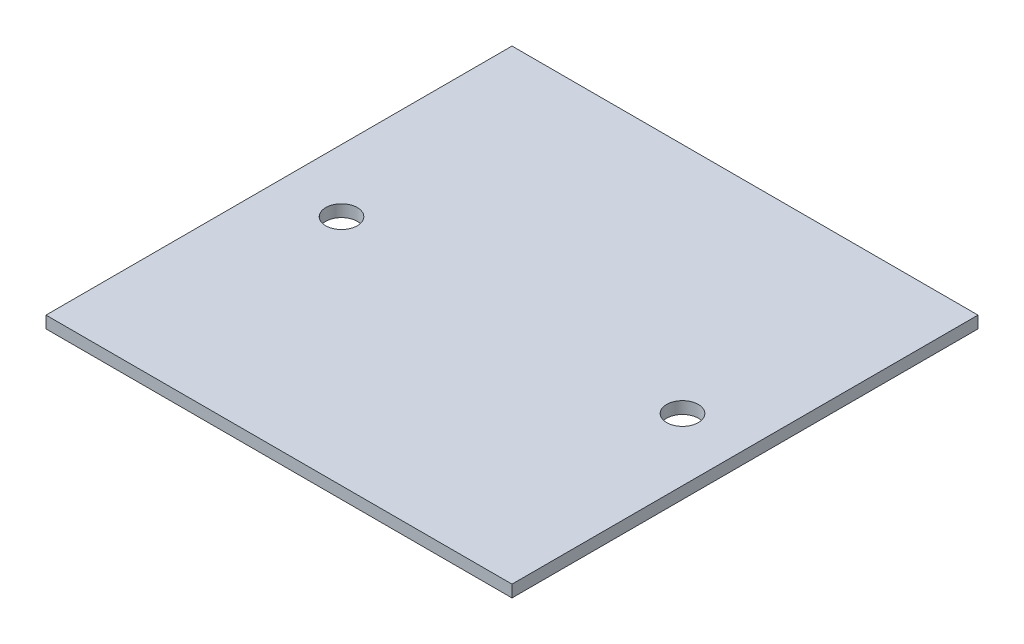
SolidWorks part; units mm, degrees
ref_plane "Alzado" through (0, 0, 0) normal (0, 0, 1) x (1, 0, 0)
ref_plane "Planta" through (0, 0, 0) normal (0, 1, 0) x (1, 0, 0)
ref_plane "Vista lateral" through (0, 0, 0) normal (1, 0, 0) x (0, 0, -1)
sketch "Croquis1" plane through (0, 0, 0) normal (0, 1, 0) x (1, 0, 0)
  line L1 (-36.9, 36.9) -> (36.9, 36.9)
  line L2 (-36.9, 36.9) -> (-36.9, -36.9)
  line L3 (-36.9, -36.9) -> (36.9, -36.9)
  line L4 (36.9, 36.9) -> (36.9, -36.9)
  line L5 (-36.9, 36.9) -> (36.9, -36.9) construction
  line L6 (-36.9, -36.9) -> (36.9, 36.9) construction
  point P0 (0, 0)
  dimension "D1" = 73.8
  dimension "D2" = 73.8
extrude "Saliente-Extruir3" add sketch "Croquis1" along normal blind 1.9
sketch "Croquis2" plane through (0, 1.9, 0) normal (0, 1, 0) x (1, 0, 0)
  line L0 (36.9, 0) -> (-36.9, 0) construction
  line L1 (36.9, -36.9) -> (36.9, 36.9) construction
  line L2 (-36.9, 36.9) -> (-36.9, -36.9) construction
  line L3 (0, 0) -> (0, 25.6728) construction
  circle A0 centre (-27, 0) radius 2.5
  circle A1 centre (27, 0) radius 2.5
  dimension "D1" = 5
  dimension "D2" = 9.9
extrude "Cortar-Extruir1" cut sketch "Croquis2" against normal through all both
